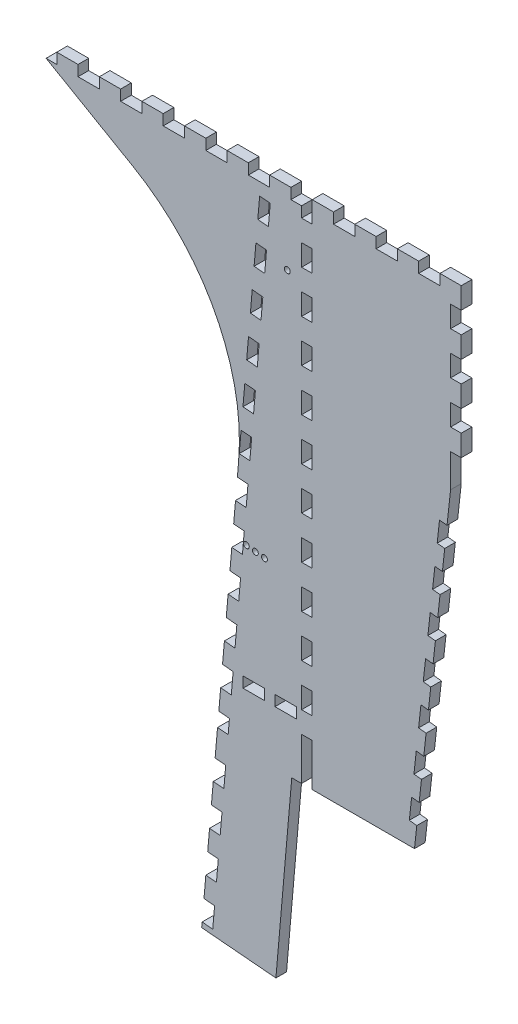
SolidWorks part; units mm, degrees
material "Pine"
ref_plane "Front Plane" through (0, 0, 0) normal (0, 0, 1) x (1, 0, 0)
ref_plane "Top Plane" through (0, 0, 0) normal (0, 1, 0) x (1, 0, 0)
ref_plane "Right Plane" through (0, 0, 0) normal (1, 0, 0) x (0, 0, -1)
sketch "Sketch1" plane through (0, 0, 0) normal (0, 0, 1) x (1, 0, 0)
  line L0 (0, 0) -> (19.9545, 228.0815)
  line L1 (145.7227, 304.8) -> (-101.9273, 304.8)
  line L2 (-101.9273, 304.8) -> (-101.9273, 298.45)
  line L3 (107.6227, 0) -> (107.6227, 304.8) construction
  line L4 (145.7227, 304.8) -> (145.7227, 0)
  line L5 (145.7227, 0) -> (0, 0)
  line L6 (44.1227, 285.75) -> (41.9532, 260.9527) construction
  line L7 (-51.1273, 304.8) -> (-51.1273, 269.1206) construction
  line L8 (-101.9273, 298.45) -> (19.9545, 228.0815)
  line L9 (41.9532, 260.9527) -> (28.3386, 105.3371) construction
  line L10 (41.9532, 260.9527) -> (28.3386, 105.3371) construction
  line L11 (41.9532, 260.9527) -> (25.6248, 105.5985) construction
  circle A0 centre (41.9532, 260.9527) radius 1.75
  circle A1 centre (28.3386, 105.3371) radius 1.75
  circle A3 centre (22.916, 105.9071) radius 1.75
  circle A5 centre (17.5165, 106.6659) radius 1.75
  circle A6 centre (25.6248, 105.5985) radius 1.75 [skipped]
  circle A7 centre (20.2129, 106.2629) radius 1.75 [skipped]
  point P13 (44.1227, 285.75)
  dimension "D10" = 3.5
  dimension "D1" = 304.8
  dimension "D2" = 101.6
  dimension "D3" = 38.1
  dimension "D4" = 85
  dimension "D5" = 19.05
  dimension "D6" = 209.55
  dimension "D8" = 6.35
  dimension "D9" = 30
  dimension "D11" = 24.892
  dimension "D12" = 19.05
  dimension "D13" = 5
  dimension "D14" = 156.21
  dimension "D16" = 1
  dimension "D15" = 5
extrude "Boss-Extrude1" add sketch "Sketch1" along normal blind 6.35 contours L2 L8 L0 L5 L4 L1 A5 A3 A1 A0
sketch "Sketch2" plane through (0, 0, 6.35) normal (0, 0, 1) x (1, 0, 0)
  line L0 (145.7227, 254) -> (117.8246, 0)
  line L3 (117.8246, 0) -> (145.7227, 0)
  line L4 (145.7227, 0) -> (145.7227, 254)
  line L6 (117.8246, 0) -> (145.7227, 27.8981) construction
  line L7 (145.7227, 27.8981) -> (145.7227, 67.3519) construction
  line L8 (145.7227, 67.3519) -> (117.8246, 95.25) construction
  line L9 (117.8246, 95.25) -> (78.3707, 95.25) construction
  line L10 (78.3707, 95.25) -> (50.4727, 67.3519) construction
  line L11 (50.4727, 67.3519) -> (50.4727, 27.8981) construction
  line L12 (50.4727, 27.8981) -> (78.3707, 0) construction
  line L13 (78.3707, 0) -> (117.8246, 0) construction
  circle A0 centre (98.0977, 47.625) radius 47.625 construction
  dimension "D1" = 254
  dimension "D3" = 95.25
extrude "Cut-Extrude1" cut sketch "Sketch2" against normal through all
sketch "Sketch5" plane through (0, 0, 6.35) normal (0, 0, 1) x (1, 0, 0)
  line L1 (120.3227, 304.8) -> (133.0227, 304.8)
  line L2 (120.3227, 304.8) -> (120.3227, 298.45)
  line L3 (120.3227, 298.45) -> (133.0227, 298.45)
  line L4 (133.0227, 304.8) -> (133.0227, 298.45)
  line L6 (145.7227, 304.8) -> (145.7227, 254) construction
  line L7 (145.7227, 304.8) -> (-101.9273, 304.8) construction
  dimension "D1" = 12.7
  dimension "D2" = 12.7
  dimension "D3" = 6.35
extrude "Cut-Extrude3" cut sketch "Sketch5" against normal through all
fillet "Fillet1" radius 127 1 edges at (19.9545, 228.0815, 3.175)
pattern_linear "LPattern1" count 10 spacing 25.4 along (-1, 0, 0) of "Cut-Extrude3"
sketch "Sketch6" plane through (0, 0, 6.35) normal (0, 0, 1) x (1, 0, 0)
  line L1 (145.7227, 292.1) -> (139.3727, 292.1)
  line L2 (145.7227, 292.1) -> (145.7227, 279.4)
  line L3 (145.7227, 279.4) -> (139.3727, 279.4)
  line L4 (139.3727, 292.1) -> (139.3727, 279.4)
  line L8 (145.7227, 304.8) -> (145.7227, 254) construction
  line L9 (145.7227, 304.8) -> (133.0227, 304.8) construction
  line L10 (120.3227, 298.45) -> (133.0227, 298.45) construction
  line L11 (133.0227, 298.45) -> (133.0227, 304.8) construction
  dimension "D1" = 12.7
extrude "Cut-Extrude4" cut sketch "Sketch6" against normal through all
sketch3d "3DSketch1"
  line L0 (145.7227, 254, 6.35) -> (145.7227, 25.2482, 6.35) construction
  line L1 (120.5977, 25.2482, 6.35) -> (145.7227, 25.2482, 6.35) construction
  line L2 (145.7227, 25.2482, 6.35) -> (145.7227, 25.2482, -18.7749) construction
  line L3 (120.5977, 25.2482, 6.35) -> (145.7227, 25.2482, -18.7749) construction
  line L4 (120.5977, 25.2482, 6.35) -> (119.2111, 12.6241, 6.35) construction
  line L5 (119.2111, 12.6241, 6.35) -> (144.3361, 12.6241, -18.7749) construction
  line L6 (144.3361, 12.6241, -18.7749) -> (145.7227, 25.2482, -18.7749) construction
  line L8 (119.2111, 12.6241, 6.35) -> (114.7345, 13.1158, 1.8734) construction
  line L9 (145.7227, 254, 6.35) -> (117.8246, 0, 6.35) construction
  dimension "D1" = 6.35
  dimension "D2" = 12.7
  dimension "D3" = 12.7
sketch "Sketch8" plane through (0, 0, 6.35) normal (0, 0, 1) x (1, 0, 0)
  line L0 (119.2111, 12.6241) -> (120.5977, 25.2482)
  line L1 (119.2111, 12.6241) -> (114.7345, 13.1158)
  line L2 (145.7227, 254) -> (117.8246, 0) construction
  line L3 (114.7345, 13.1158) -> (116.1211, 25.7399)
  line L5 (116.1211, 25.7399) -> (120.5977, 25.2482)
  dimension "D1" = 12.7
  dimension "D2" = 12.7
extrude "Cut-Extrude5" cut sketch "Sketch8" against normal through all
pattern_linear "LPattern3" count 7 spacing 25.4 along (0.1092, 0.994, 0) of "Cut-Extrude5"
sketch "Sketch10" plane through (0, 0, 6.35) normal (0, 0, 1) x (1, 0, 0)
  line L0 (145.7227, 254) -> (137.2365, 176.7371) construction
  line L1 (145.7227, 279.4) -> (139.3727, 279.4)
  line L2 (145.7227, 279.4) -> (145.7227, 196.186)
  line L3 (145.7227, 196.186) -> (139.3727, 196.186)
  line L4 (139.3727, 279.4) -> (139.3727, 196.186)
extrude "Boss-Extrude2" add sketch "Sketch10" against normal through all
pattern_linear "LPattern4" count 4 spacing 25.4 along (0, -1, 0) of "Cut-Extrude4"
sketch "Sketch11" plane through (0, 0, 6.35) normal (0, 0, 1) x (1, 0, 0)
  line L0 (139.3727, 203.2) -> (145.7227, 203.2) construction
  line L1 (139.3727, 203.2) -> (145.7227, 203.2)
  line L2 (139.3727, 203.2) -> (139.3727, 196.186)
  line L3 (139.3727, 196.186) -> (145.7227, 196.186)
  line L4 (145.7227, 203.2) -> (145.7227, 196.186)
  line L5 (139.3727, 196.186) -> (145.7227, 196.186) construction
extrude "Cut-Extrude7" cut sketch "Sketch11" against normal through all
sketch "Sketch12" plane through (0, 0, 6.35) normal (0, 0, 1) x (1, 0, 0)
  line L1 (56.8227, 25.4) -> (50.4727, 25.4)
  line L2 (56.8227, 25.4) -> (56.8227, 12.7)
  line L3 (56.8227, 12.7) -> (50.4727, 12.7)
  line L4 (50.4727, 25.4) -> (50.4727, 12.7)
  line L6 (145.7227, 254) -> (145.7227, 241.3) construction
  line L7 (117.8246, 0) -> (0, 0) construction
  dimension "D1" = 88.9
  dimension "D2" = 6.35
  dimension "D3" = 12.7
  dimension "D4" = 12.7
extrude "Cut-Extrude8" cut sketch "Sketch12" against normal through all
pattern_linear "LPattern5" count 12 spacing 25.4 along (0, 1, 0) of "Cut-Extrude8"
sketch "Sketch13" plane through (0, 0, 6.35) normal (0, 0, 1) x (1, 0, 0)
  line L0 (0, 0) -> (1.1069, 12.6517)
  line L1 (0, 0) -> (6.3258, -0.5534)
  line L2 (1.1069, 12.6517) -> (7.4327, 12.0982)
  line L3 (6.3258, -0.5534) -> (7.4327, 12.0982)
  line L5 (0, 0) -> (12.903, 147.4814) construction
  dimension "D1" = 12.7
  dimension "D3" = 6.35
extrude "Cut-Extrude9" cut sketch "Sketch13" against normal through all
pattern_linear "LPattern6" count 12 spacing 25.4 along (0.0872, 0.9962, 0) of "Cut-Extrude9"
sketch "Sketch15" plane through (0, 0, 6.35) normal (0, 0, 1) x (1, 0, 0)
  line L0 (50.4727, 50.8) -> (50.4727, 38.1) construction
  line L1 (47.2977, 31.75) -> (34.5977, 31.75)
  line L2 (47.2977, 31.75) -> (47.2977, 38.1)
  line L3 (47.2977, 38.1) -> (34.5977, 38.1)
  line L4 (34.5977, 31.75) -> (34.5977, 38.1)
  line L6 (28.2477, 31.75) -> (15.5477, 31.75)
  line L7 (28.2477, 31.75) -> (28.2477, 38.1)
  line L8 (28.2477, 38.1) -> (15.5477, 38.1)
  line L9 (15.5477, 31.75) -> (15.5477, 38.1)
  line L12 (50.4727, 38.1) -> (56.8227, 38.1) construction
  dimension "D1" = 3.175
  dimension "D2" = 6.35
  dimension "D3" = 6.35
extrude "Cut-Extrude10" cut sketch "Sketch15" against normal through all
sketch "Sketch16" plane through (0, 0, 6.35) normal (0, 0, 1) x (1, 0, 0)
  line L1 (50.4727, 12.7) -> (56.8227, 12.7)
  line L2 (50.4727, 12.7) -> (50.4727, 0)
  line L3 (50.4727, 0) -> (56.8227, 0)
  line L4 (56.8227, 12.7) -> (56.8227, 0)
  line L6 (117.8246, 0) -> (6.3743, 0) construction
extrude "Cut-Extrude11" cut sketch "Sketch16" against normal through all
sketch "Sketch20" plane through (0, 0, 6.35) normal (0, 0, 1) x (1, 0, 0)
  line L0 (0.3389, 3.8741) -> (44.6198, 0)
  line L1 (0.3389, 3.8741) -> (-9.1238, -104.2855)
  line L2 (44.6198, 0) -> (35.1571, -108.1595)
  line L3 (-9.1238, -104.2855) -> (35.1571, -108.1595)
  line L4 (3.3206, 37.955) -> (4.4275, 50.6067) construction
  line L5 (50.4727, 0) -> (6.3743, 0) construction
  circle A0 centre (41.9532, 260.9527) radius 1.75 construction
  dimension "D1" = 368.3
  dimension "D2" = 44.45
extrude "Boss-Extrude4" add sketch "Sketch20" against normal blind 6.35
pattern_linear "LPattern7" count 5 spacing 25.4 along (-0.0872, -0.9962, 0) of "Cut-Extrude9"
sketch "Sketch22" plane through (0, 0, 6.35) normal (0, 0, 1) x (1, 0, 0)
  line L0 (36.5327, -92.4358) -> (35.4258, -105.0875)
  line L1 (36.5327, -92.4358) -> (30.2069, -91.8823)
  line L2 (35.4258, -105.0875) -> (29.1, -104.534)
  line L3 (30.2069, -91.8823) -> (29.1, -104.534)
  line L4 (35.1571, -108.1595) -> (44.6198, 0) construction
  line L5 (-1.4223, -89.1151) -> (-7.7481, -88.5617) construction
  line L6 (-0.3154, -76.4635) -> (0.7914, -63.8118) construction
  line L7 (-6.6413, -75.91) -> (-0.3154, -76.4635) construction
equation "\".25i\"=10"
